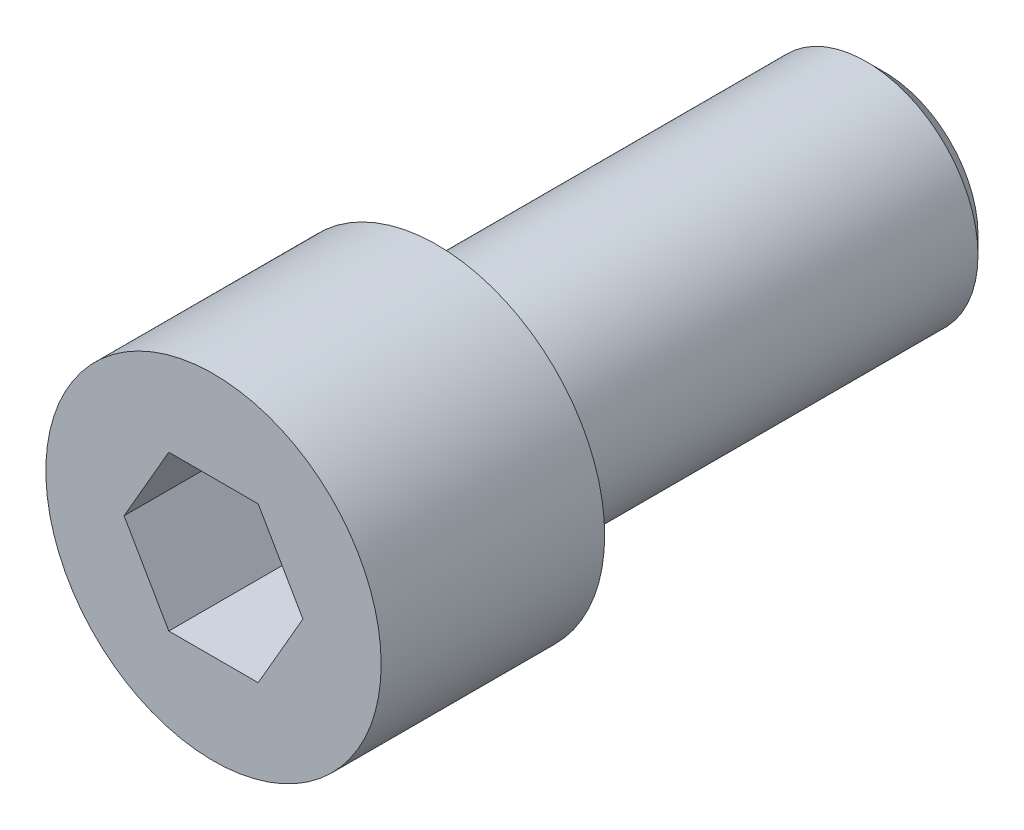
SolidWorks part; units mm, degrees
ref_plane "Front Plane" through (0, 0, 0) normal (0, 0, 1) x (1, 0, 0)
ref_plane "Top Plane" through (0, 0, 0) normal (0, 1, 0) x (1, 0, 0)
ref_plane "Right Plane" through (0, 0, 0) normal (1, 0, 0) x (0, 0, -1)
sketch "Sketch1" plane through (0, 0, 0) normal (0, 1, 0) x (1, 0, 0)
  line L1 (0, 0) -> (1.875, 0)
  line L2 (0, 0) -> (0, 2.5)
  line L3 (0, 2.5) -> (1.875, 2.5)
  line L4 (1.875, 0) -> (1.875, 2.5)
  line L5 (0, 2.5) -> (1.25, 2.5)
  line L6 (0, 2.5) -> (0, 7.5)
  line L7 (0, 7.5) -> (1.25, 7.5)
  line L8 (1.25, 2.5) -> (1.25, 7.5)
  dimension "D1" = 2.5
  dimension "D2" = 5
  dimension "D3" = 1.25
  dimension "D4" = 1.875
revolve "Revolve1" add sketch "Sketch1" angle 360 about L6
sketch "Sketch2" plane through (0, 0, 0) normal (0, 0, 1) x (1, 0, 0)
  line L0 (0, 0) -> (1.875, 0) construction
  line L1 (1, 0) -> (0.5, 0.866)
  line L2 (0.5, 0.866) -> (-0.5, 0.866)
  line L3 (-0.5, 0.866) -> (-1, 0)
  line L4 (-1, 0) -> (-0.5, -0.866)
  line L5 (-0.5, -0.866) -> (0.5, -0.866)
  line L6 (0.5, -0.866) -> (1, 0)
  line L7 (0, 0) -> (-1.875, 0) construction
  line L8 (0, 0) -> (0, 1.875) construction
  line L9 (0, 0) -> (0, -1.875) construction
  circle A0 centre (0, 0) radius 0.866 construction
  circle A1 centre (0, 0) radius 1.875 construction
  dimension "D1" = 2
extrude "Cut-Extrude1" cut sketch "Sketch2" against normal blind 1.5
fillet "Fillet1" radius 0.15 1 edges at (1.25, 0, -2.5)
chamfer "Chamfer1" distance 0.2 angle 45 1 edges at (1.25, 0, -7.5)
